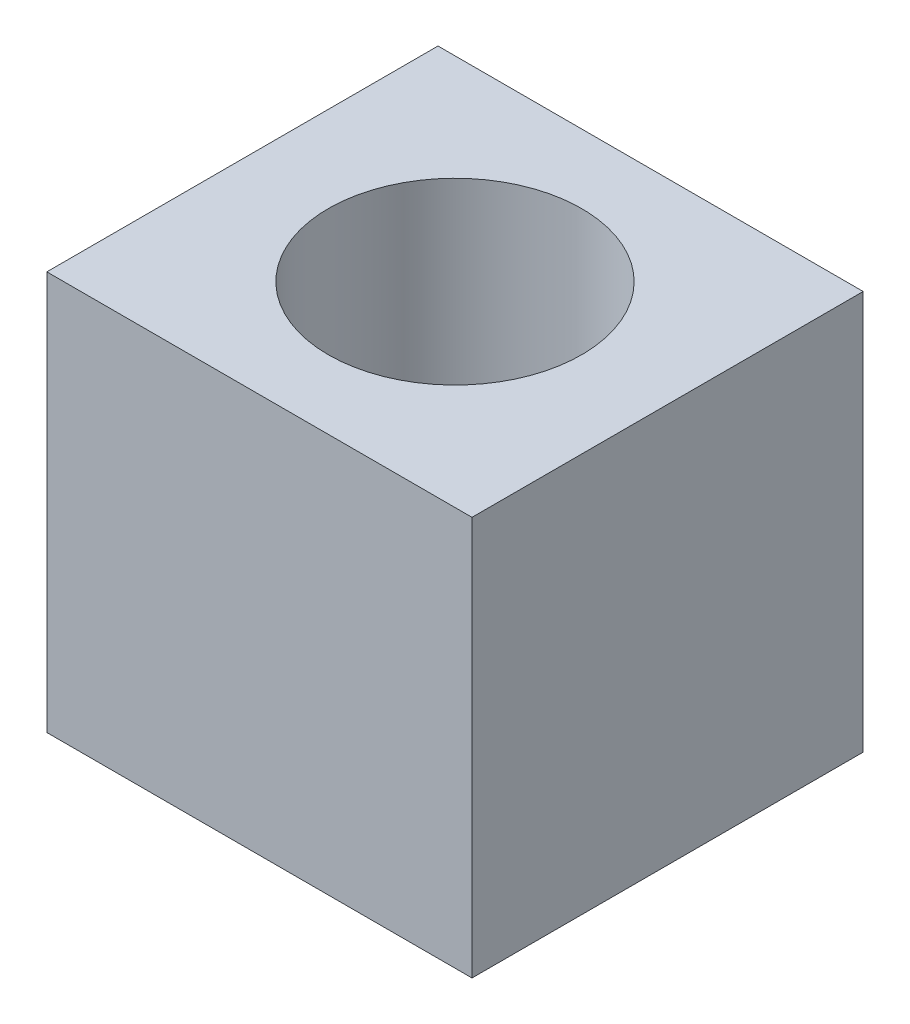
SolidWorks part; units mm, degrees
ref_plane "Front Plane" through (0, 0, 0) normal (0, 0, 1) x (1, 0, 0)
ref_plane "Top Plane" through (0, 0, 0) normal (0, 1, 0) x (1, 0, 0)
ref_plane "Right Plane" through (0, 0, 0) normal (1, 0, 0) x (0, 0, -1)
sketch "Sketch1" plane through (0, 0, 0) normal (0, 1, 0) x (1, 0, 0)
  line L1 (-10.6572, 9.8046) -> (10.6572, 9.8046)
  line L2 (-10.6572, 9.8046) -> (-10.6572, -9.8046)
  line L3 (-10.6572, -9.8046) -> (10.6572, -9.8046)
  line L4 (10.6572, 9.8046) -> (10.6572, -9.8046)
  line L5 (-10.6572, 9.8046) -> (10.6572, -9.8046) construction
  line L6 (-10.6572, -9.8046) -> (10.6572, 9.8046) construction
  circle A0 centre (0, 0) radius 6.35
extrude "Boss-Extrude1" add sketch "Sketch1" along normal blind 20
